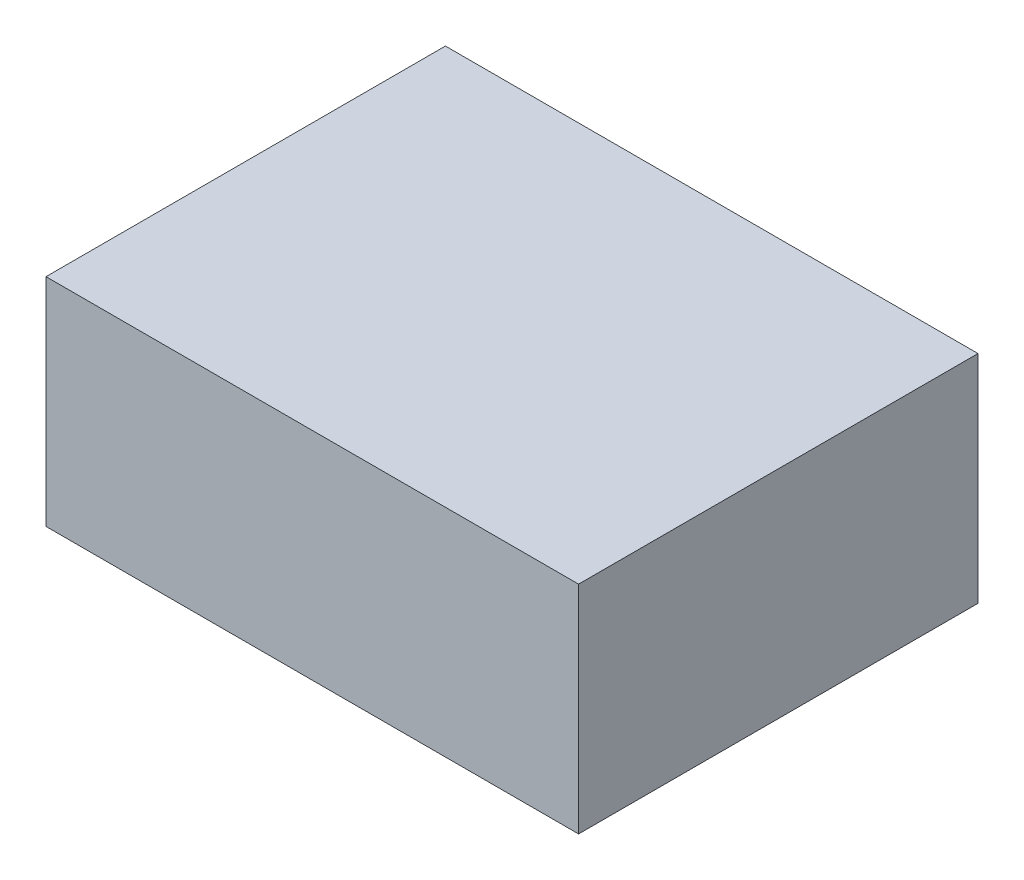
SolidWorks part; units mm, degrees
ref_plane "Front Plane" through (0, 0, 0) normal (0, 0, 1) x (1, 0, 0)
ref_plane "Top Plane" through (0, 0, 0) normal (0, 1, 0) x (1, 0, 0)
ref_plane "Right Plane" through (0, 0, 0) normal (1, 0, 0) x (0, 0, -1)
sketch "Sketch1" plane through (0, 0, 0) normal (0, 1, 0) x (1, 0, 0)
  line L1 (-203.2, 152.4) -> (203.2, 152.4)
  line L2 (-203.2, 152.4) -> (-203.2, -152.4)
  line L3 (-203.2, -152.4) -> (203.2, -152.4)
  line L4 (203.2, 152.4) -> (203.2, -152.4)
  line L5 (-203.2, 152.4) -> (203.2, -152.4) construction
  line L6 (-203.2, -152.4) -> (203.2, 152.4) construction
  point P0 (0, 0)
  dimension "D1" = 406.4
  dimension "D2" = 304.8
extrude "Boss-Extrude1" add sketch "Sketch1" along normal blind 165.1
